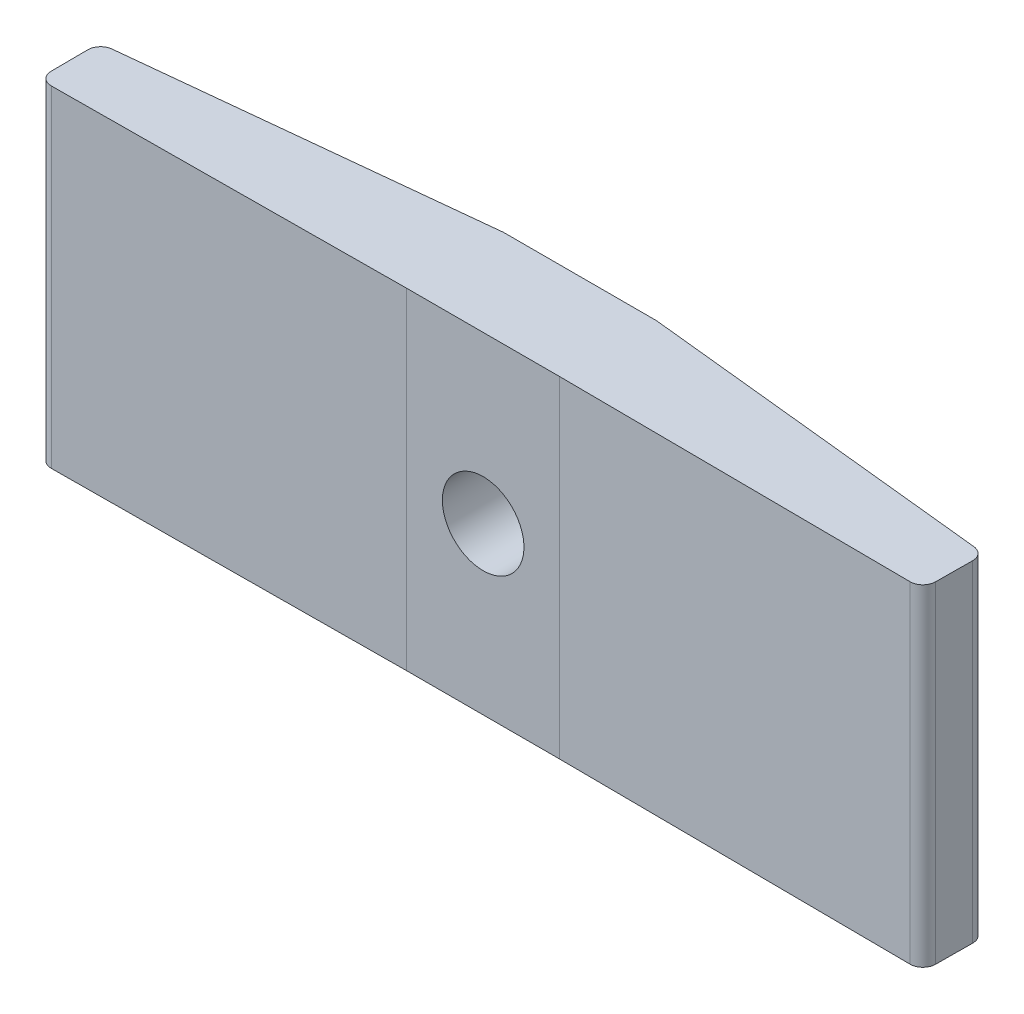
SolidWorks part; units mm, degrees
ref_plane "Front" through (0, 0, 0) normal (0, 0, 1) x (1, 0, 0)
ref_plane "Top" through (0, 0, 0) normal (0, 1, 0) x (1, 0, 0)
ref_plane "Right" through (0, 0, 0) normal (1, 0, 0) x (0, 0, -1)
sketch "Sketch1" plane through (0, 0, 0) normal (0, 1, 0) x (1, 0, 0)
  line L0 (0, 0) -> (34.7, 0) construction
  line L1 (17.35, 0) -> (17.35, 17.8266) construction
  line L2 (20.35, 0.1) -> (14.35, 0.1)
  line L3 (14.35, 0.1) -> (0, 0)
  line L4 (0, 0) -> (-0.0167, 2.4)
  line L9 (20.35, 3.9) -> (34.7167, 2.4)
  line L10 (20.35, 3.9) -> (14.35, 3.9)
  line L11 (14.35, 3.9) -> (-0.0167, 2.4)
  line L14 (34.7, 0) -> (34.7167, 2.4)
  line L15 (20.35, 0.1) -> (34.7, 0)
  line L16 (14.35, 3.9) -> (14.35, 0.1) construction
  point P25 (17.35, 3.9)
  point P26 (17.35, 2.4)
  point P28 (17.35, 2.2)
  point P29 (17.35, 0.1)
  dimension "D1" = 34.7
  dimension "D2" = 0.2
  dimension "D3" = 3.8
  dimension "D4" = 1.5
  dimension "D6" = 6
  dimension "D8" = 2.4
extrude "Boss-Extrude1" add sketch "Sketch1" along normal blind 13
fillet "Fillet1" [suppressed] radius 0.1
fillet "Fillet2" radius 0.5 4 edges at (-0.0167, 6.5, -2.4) (34.7167, 6.5, -2.4) (34.7, 6.5, 0) (0, 6.5, 0)
sketch "Sketch2" plane through (0, 0, -3.9) normal (0, 0, -1) x (-1, 0, 0)
  line L0 (-17.35, 6.5) -> (-17.35, 0) construction
  line L1 (-20.35, 0) -> (-14.35, 0) construction
  line L2 (-17.35, 6.5) -> (-17.35, 13) construction
  line L3 (-20.35, 13) -> (-14.35, 13) construction
  circle A0 centre (-17.35, 6.5) radius 1.6
  dimension "D1" = 3.2
extrude "Cut-Extrude1" cut sketch "Sketch2" against normal through all
sketch "Sketch3" plane through (0.6222, 0, -5.9597) normal (0.1038, 0, -0.9946) x (-0.9946, 0, -0.1038)
  line L0 (-33.8261, 1) -> (-19.835, 1) construction
  line L1 (-33.8261, 13) -> (-33.8261, 0) construction
  line L2 (-19.835, 13) -> (-19.835, 0) construction
  line L4 (-33.8261, 0) -> (-19.835, 0) construction
  text T0 "BCL" font "Century Gothic" height in points 20
  dimension "D1" = 1
extrude "Boss-Extrude2" [suppressed] add sketch "Sketch3" along normal blind 0.4
sketch "Sketch4" plane through (-0.2481, 0, -2.3758) normal (-0.1038, 0, -0.9946) x (-0.9946, 0, 0.1038)
  line L0 (-14.6774, 1) -> (-0.6863, 1) construction
  line L1 (-14.6774, 13) -> (-14.6774, 0) construction
  line L2 (-0.6863, 0) -> (-0.6863, 13) construction
  line L3 (-14.6774, 0) -> (-0.6863, 0) construction
  text T0 "02" font "Century Gothic" height in points 20
  dimension "D1" = 1
extrude "Boss-Extrude3" [suppressed] add sketch "Sketch4" along normal blind 0.4
sketch "Sketch5" plane through (-0.2481, 0, -2.3758) normal (-0.1038, 0, -0.9946) x (-0.9946, 0, 0.1038)
  line L0 (-14.6774, 1) -> (-0.6863, 1) construction
  line L1 (-14.6774, 13) -> (-14.6774, 0) construction
  line L2 (-0.6863, 0) -> (-0.6863, 13) construction
  line L3 (-14.6774, 0) -> (-0.6863, 0) construction
  text T0 "...."
  dimension "D1" = 1
extrude "revision indication" add sketch "Sketch5" along normal blind 0.4
